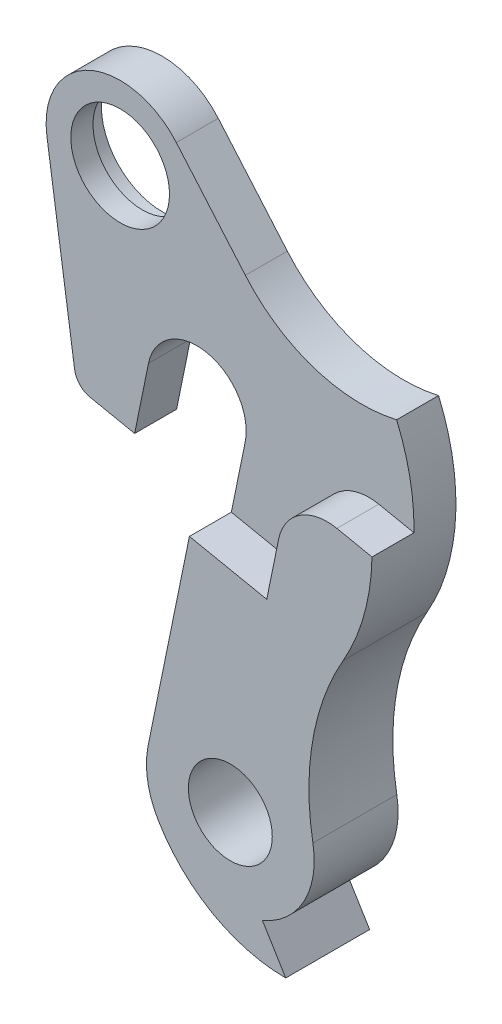
SolidWorks part; units mm, degrees
ref_plane "Plan de face" through (0, 0, 0) normal (0, 0, 1) x (1, 0, 0)
ref_plane "Plan de dessus" through (0, 0, 0) normal (0, 1, 0) x (1, 0, 0)
ref_plane "Plan de droite" through (0, 0, 0) normal (1, 0, 0) x (0, 0, -1)
sketch "Esquisse33" plane through (0, 0, 0) normal (0, 0, 1) x (1, 0, 0)
  line L0 (1.7552, 8.5814) -> (-1.842, -9.0056) construction
  line L1 (0, 0) -> (0, -5.2715) construction
  line L2 (18.0186, -3.6855) -> (-24.914, 5.0959) construction
  line L3 (10.8918, -37.8548) -> (13.258, -41.725)
  line L16 (-10.8059, -4.9347) -> (-6.3013, -5.8561)
  line L17 (-15.1911, 15.808) -> (-12.3838, -3.2665)
  line L18 (4.9173, 13.6305) -> (-2.0792, 21.7841)
  line L22 (4.8986, -1.002) -> (-0.6843, -28.2967)
  line L23 (-6.3013, -5.8561) -> (-4.8986, 1.002)
  arc A0 (-12.3838, -3.2665) -> (-10.8059, -4.9347) centre (-10.4051, -2.9753) ccw
  arc A1 (-0.6843, -28.2967) -> (0.3011, -34.2827) centre (7.6433, -30) ccw
  arc A2 (0.3011, -34.2827) -> (13.258, -41.725) centre (13.258, -26.725) ccw
  arc A3 (19.0695, -10.9706) -> (16.011, -28.5059) centre (41.6062, -23.9359) ccw
  arc A4 (10.8918, -37.8548) -> (16.011, -28.5059) centre (7.6433, -30) ccw
  arc A13 (-2.0792, 21.7841) -> (-15.1911, 15.808) centre (-7.771, 16.9) ccw
  arc A14 (4.9173, 13.6305) -> (20.2415, 8.6186) centre (16.7079, 23.7479) ccw
  arc A15 (19.0695, -10.9706) -> (20.2415, 8.6186) centre (0, 0) ccw
  arc A17 (4.8986, -1.002) -> (-4.8986, 1.002) centre (0, 0) ccw
  point P14 (-12.1796, -4.6537)
  dimension "D1" = 22
  dimension "D2" = 5
  dimension "D6" = 7.5
  dimension "D10" = 11
  dimension "D11" = 2
  dimension "D12" = 8.5
  dimension "D15" = 8.5
  dimension "D16" = 30
  dimension "D17" = 26
  dimension "D18" = 30
  dimension "D19" = 13
  dimension "D3" = 11.56
  dimension "D7" = 15
  dimension "D8" = 11
  dimension "D9" = 7
  dimension "D13" = 19.5
  dimension "D14" = 32.26
  dimension "D20" = 43
extrude "Extrusion12" add sketch "Esquisse33" along normal mid plane 8.5
sketch "Esquisse34" plane through (0, 0, 0) normal (0, 0, 1) x (1, 0, 0)
  line L3 (3.4958, -7.86) -> (11.3336, -9.4631)
  line L4 (11.3336, -9.4631) -> (12.5359, -3.5848)
  line L5 (18.4365, 0.3118) -> (21.9961, -0.4163)
  line L9 (-6.3013, -5.8561) -> (-4.8986, 1.002)
  line L10 (4.8986, -1.002) -> (-0.6843, -28.2967)
  line L11 (13.258, -41.725) -> (10.8918, -37.8548)
  line L12 (4.9173, 13.6305) -> (-2.0792, 21.7841)
  line L13 (-15.1911, 15.808) -> (-12.3838, -3.2665)
  line L14 (-10.8059, -4.9347) -> (-6.3013, -5.8561)
  line L15 (-6.3013, -5.8561) -> (-4.8986, 1.002)
  line L16 (4.8986, -1.002) -> (3.4958, -7.86)
  line L18 (4.9173, 13.6305) -> (-2.0792, 21.7841)
  line L19 (-15.1911, 15.808) -> (-12.3838, -3.2665)
  line L20 (-10.8059, -4.9347) -> (-6.3013, -5.8561)
  arc A1 (18.4365, 0.3118) -> (12.5359, -3.5848) centre (17.4345, -4.5868) ccw
  arc A11 (4.8986, -1.002) -> (-4.8986, 1.002) centre (0, 0) ccw
  arc A12 (-0.6843, -28.2967) -> (0.3011, -34.2827) centre (7.6433, -30) ccw
  arc A13 (0.3011, -34.2827) -> (13.258, -41.725) centre (13.258, -26.725) ccw
  arc A14 (10.8918, -37.8548) -> (16.011, -28.5059) centre (7.6433, -30) ccw
  arc A15 (19.0695, -10.9706) -> (16.011, -28.5059) centre (41.6062, -23.9359) ccw
  arc A16 (19.0695, -10.9706) -> (20.2415, 8.6186) centre (0, 0) ccw
  arc A17 (4.9173, 13.6305) -> (20.2415, 8.6186) centre (16.7079, 23.7479) ccw
  arc A18 (-2.0792, 21.7841) -> (-15.1911, 15.808) centre (-7.771, 16.9) ccw
  arc A19 (-12.3838, -3.2665) -> (-10.8059, -4.9347) centre (-10.4051, -2.9753) ccw
  arc A20 (4.8986, -1.002) -> (-4.8986, 1.002) centre (0, 0) ccw
  arc A25 (21.9961, -0.4163) -> (20.2415, 8.6186) centre (0, 0) ccw
  arc A26 (4.9173, 13.6305) -> (20.2415, 8.6186) centre (16.7079, 23.7479) ccw
  arc A27 (-2.0792, 21.7841) -> (-15.1911, 15.808) centre (-7.771, 16.9) ccw
  arc A28 (-12.3838, -3.2665) -> (-10.8059, -4.9347) centre (-10.4051, -2.9753) ccw
  point P8 (0, 0)
  dimension "D2" = 5
  dimension "D3" = 8
  dimension "D4" = 11
  dimension "D1" = 0
extrude "Enlèv. mat.-Extru.13" cut sketch "Esquisse34" along normal through all
sketch "Esquisse35" plane through (0, 0, 0) normal (0, 0, 1) x (1, 0, 0)
  circle A0 centre (-7.771, 16.9) radius 5
  arc A1 (-2.0792, 21.7841) -> (-15.1911, 15.808) centre (-7.771, 16.9) ccw construction
  circle A2 centre (7.6433, -30) radius 4.25
  arc A3 (10.8918, -37.8548) -> (16.011, -28.5059) centre (7.6433, -30) ccw construction
  dimension "D1" = 10
  dimension "D2" = 8.5
extrude "Enlèv. mat.-Extru.14" cut sketch "Esquisse35" against normal through all and the other way through all
sketch "Esquisse36" plane through (0, 0, -4.25) normal (0, 0, -1) x (-1, 0, 0)
  circle A0 centre (7.771, 16.9) radius 6.15
  circle A1 centre (7.771, 16.9) radius 5 construction
  dimension "D1" = 12.3
extrude "Enlèv. mat.-Extru.15" cut sketch "Esquisse36" against normal blind 2
